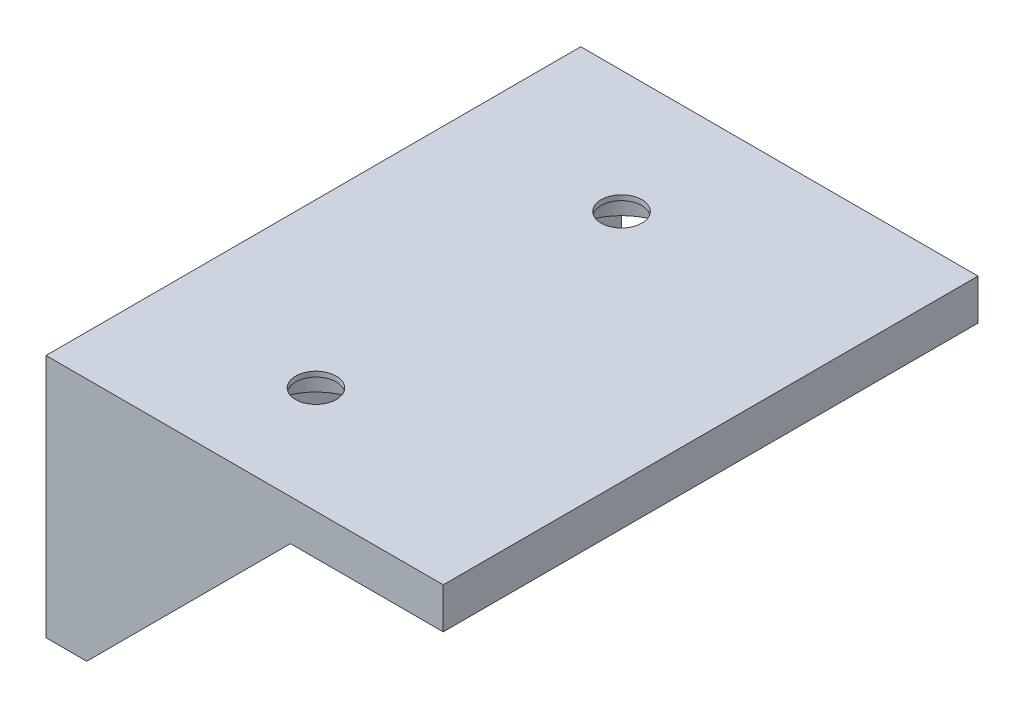
SolidWorks part; units mm, degrees
ref_plane "Plano frontal" through (0, 0, 0) normal (0, 0, 1) x (1, 0, 0)
ref_plane "Plano superior" through (0, 0, 0) normal (0, 1, 0) x (1, 0, 0)
ref_plane "Plano direito" through (0, 0, 0) normal (1, 0, 0) x (0, 0, -1)
sketch "Esboço1" plane through (0, 0, 0) normal (0, 0, 1) x (1, 0, 0)
  line L0 (0, 0) -> (35, 0)
  line L1 (35, 0) -> (35, 4)
  line L2 (35, 4) -> (-4, 4)
  line L3 (-4, 4) -> (-4, -20)
  line L4 (-4, -20) -> (0, -20)
  line L5 (0, -20) -> (0, 0)
  dimension "D1" = 4
  dimension "D2" = 35
  dimension "D3" = 20
extrude "Ressalto-extrusão1" add sketch "Esboço1" along normal blind 50
sketch "Esboço2" plane through (0, 0, 0) normal (1, 0, 0) x (0, 0, -1)
  line L0 (-27, 0) -> (-27, -20) construction
  line L1 (-50, 0) -> (0, 0) construction
  line L3 (-50, -20) -> (-50, 0) construction
  circle A0 centre (-42, -12) radius 5.15
  circle A1 centre (-12, -12) radius 5.15
  point P10 (-50, -10)
  dimension "D1" = 10.3
  dimension "D2" = 30
  dimension "D3" = 12
  dimension "D4" = 23
extrude "Corte-extrusão1" cut sketch "Esboço2" against normal blind 3.5
sketch "Esboço3" plane through (0, 0, 0) normal (0, -1, 0) x (1, 0, 0)
  line L0 (35, 27) -> (0, 27) construction
  line L2 (0, 50) -> (0, 0) construction
  line L3 (0, 50) -> (35, 50) construction
  circle A0 centre (12, 42) radius 5.15
  circle A1 centre (12, 12) radius 5.15
  dimension "D2" = 10.3
  dimension "D1" = 12
  dimension "D3" = 30
  dimension "D4" = 23
extrude "Corte-extrusão2" cut sketch "Esboço3" against normal blind 3.5
sketch "Esboço4" plane through (0, 0, 50) normal (0, 0, 1) x (1, 0, 0)
  line L0 (0, -20) -> (20, 0)
  line L1 (35, 0) -> (35, 4) construction
  line L2 (35, 4) -> (-4, 4)
  line L3 (-4, 4) -> (-4, -20)
  line L4 (-4, -20) -> (0, -20)
  line L5 (0, 0) -> (35, 0) construction
  line L6 (20, 0) -> (35, 0)
  line L7 (35, 0) -> (35, 4)
  dimension "D1" = 45
extrude "Ressalto-extrusão2" add sketch "Esboço4" along normal blind 2.5
sketch "Esboço5" plane through (0, 3.5, 0) normal (0, -1, 0) x (1, 0, 0)
  circle A0 centre (12, 42) radius 2
  circle A1 centre (12, 12) radius 2
  dimension "D1" = 4
extrude "Corte-extrusão3" cut sketch "Esboço5" against normal blind 10
sketch "Esboço6" plane through (-3.5, 0, 0) normal (1, 0, 0) x (0, 0, -1)
  circle A0 centre (-42, -12) radius 2
  circle A1 centre (-12, -12) radius 2
  dimension "D1" = 4
extrude "Corte-extrusão4" cut sketch "Esboço6" against normal blind 10
